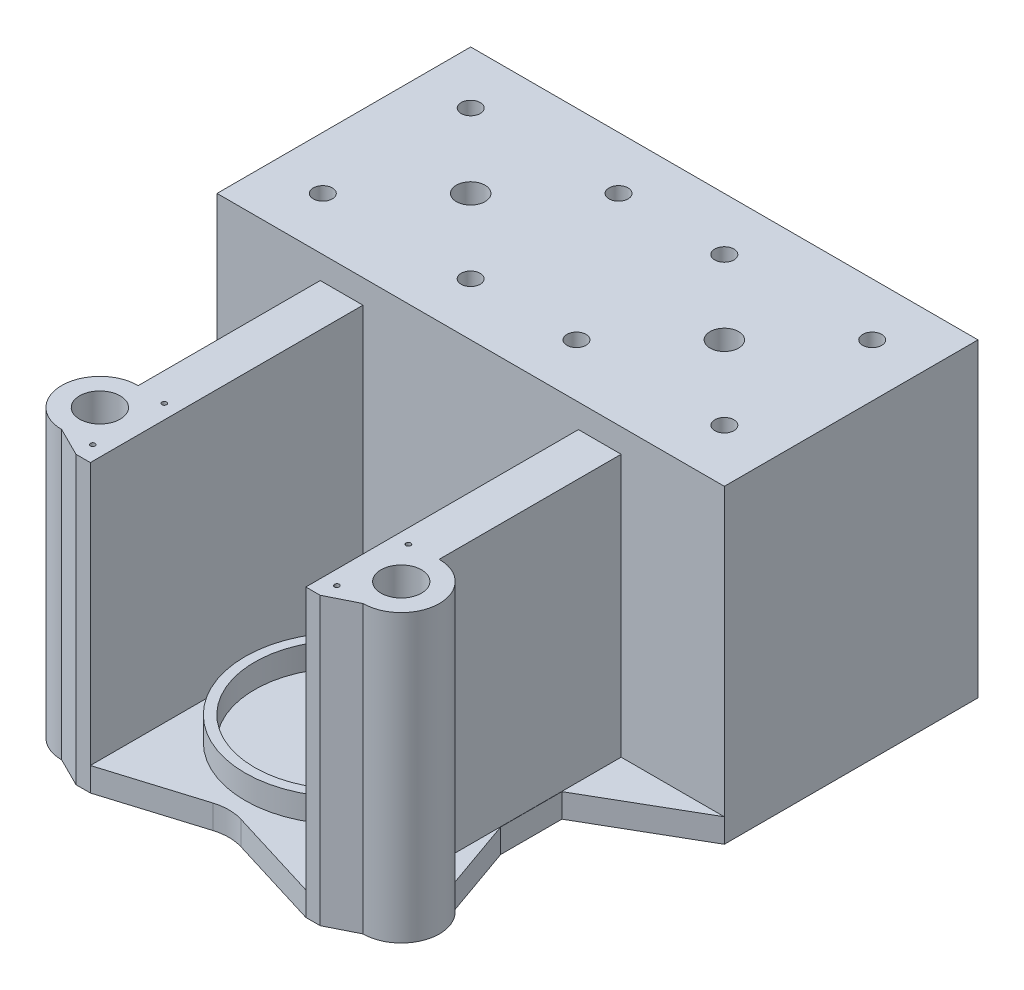
SolidWorks part; units mm, degrees
ref_plane "Front Plane" through (0, 0, 0) normal (0, 0, 1) x (1, 0, 0)
ref_plane "Top Plane" through (0, 0, 0) normal (0, 1, 0) x (1, 0, 0)
ref_plane "Right Plane" through (0, 0, 0) normal (1, 0, 0) x (0, 0, -1)
sketch "Sketch1" plane through (0, 0, 0) normal (0, 1, 0) x (1, 0, 0)
  circle A0 centre (0, 0) radius 21.15
  dimension "D1" = 42.3
extrude "Boss-Extrude1" add sketch "Sketch1" along normal blind 5
sketch "Sketch2" plane through (0, 0, 0) normal (0, 1, 0) x (1, 0, 0)
  circle A0 centre (0, 0) radius 19.15
  circle A1 centre (0, 0) radius 21.15
  dimension "D1" = 38.3
  dimension "D2" = 42.3
extrude "Boss-Extrude2" add sketch "Sketch2" along normal blind 10
sketch "Sketch3" plane through (0, 0, 0) normal (0, 1, 0) x (1, 0, 0)
  line L0 (48.18, 31.15) -> (5, 31.15)
  line L1 (-5, 74.33) -> (-48.18, 74.33)
  line L2 (-5, 74.33) -> (-5, 31.15)
  line L3 (-5, 31.15) -> (-48.18, 31.15)
  line L4 (-48.18, 74.33) -> (-48.18, 31.15)
  line L5 (-5, 74.33) -> (-48.18, 31.15) construction
  line L6 (-5, 31.15) -> (-48.18, 74.33) construction
  line L7 (5, 74.33) -> (5, 31.15)
  line L8 (48.18, 74.33) -> (5, 74.33)
  line L9 (48.18, 74.33) -> (48.18, 31.15)
  line L10 (0, 0) -> (0, 74.33) construction
  line L11 (0, 26.15) -> (-53.18, 26.15)
  line L12 (-53.18, 79.33) -> (-53.18, 26.15)
  line L13 (0, 79.33) -> (-53.18, 79.33)
  line L14 (0, 79.33) -> (0, 26.15)
  line L15 (53.18, 26.15) -> (0, 26.15)
  line L16 (0, 79.33) -> (0, 26.15)
  line L17 (53.18, 79.33) -> (0, 79.33)
  line L18 (53.18, 79.33) -> (53.18, 26.15)
  line L19 (-36.7936, -13.9236) -> (-31.59, 0.8326)
  line L20 (-31.59, 0.8326) -> (-31.59, 13.685)
  line L21 (-31.59, 13.685) -> (-53.18, 26.15)
  line L22 (-26.3864, -26.0764) -> (0, -21.15)
  line L23 (-26.3864, -26.0764) -> (-36.7936, -13.9236) construction
  line L24 (53.18, 26.15) -> (31.59, 13.685)
  line L25 (31.59, 13.685) -> (31.59, 0.8326)
  line L26 (31.59, 0.8326) -> (36.7936, -13.9236)
  line L27 (0, -21.15) -> (26.3864, -26.0764)
  line L28 (26.3864, -26.0764) -> (36.7936, -13.9236) construction
  circle A0 centre (0, 0) radius 21.15 construction
  circle A1 centre (-31.59, -20) radius 8
  circle A2 centre (31.59, -20) radius 8
  circle A3 centre (0, 0) radius 21.15
  point P0 (-26.59, 52.74)
  point P12 (0, 21.15)
  dimension "D8" = 16
  dimension "D1" = 43.18
  dimension "D2" = 43.18
  dimension "D4" = 5
  dimension "D5" = 5
  dimension "D6" = 10
  dimension "D9" = 5
  dimension "D10" = 20
  dimension "D11" = 120
  dimension "D12" = 120
  dimension "D13" = 120
  dimension "D14" = 120
  dimension "D15" = 120
  dimension "D16" = 120
  dimension "D7" = 5
  dimension "D3" = 2
extrude "Boss-Extrude4" add sketch "Sketch3" along normal blind 5 contours A2 | A1 | L18 L17 L14 L15 L8 L9 L0 L7 | L14 L13 L12 L11 L4 L1 L2 L3 | L22 A3 L27 A2 L26 L25 L24 L15 L11 L21 L20 L19 A1 | A3
sketch "Sketch4" plane through (0, 5, 0) normal (0, 1, 0) x (1, 0, 0)
  line L0 (48.18, 31.15) -> (5, 31.15) construction
  line L1 (48.18, 74.33) -> (48.18, 31.15) construction
  line L2 (48.18, 74.33) -> (5, 74.33) construction
  line L3 (5, 74.33) -> (5, 31.15) construction
  line L4 (-5, 31.15) -> (-48.18, 31.15) construction
  line L5 (-5, 74.33) -> (-5, 31.15) construction
  line L6 (-5, 74.33) -> (-48.18, 74.33) construction
  line L7 (-48.18, 74.33) -> (-48.18, 31.15) construction
  line L8 (48.18, 31.15) -> (5, 31.15)
  line L9 (48.18, 74.33) -> (48.18, 31.15)
  line L10 (48.18, 74.33) -> (5, 74.33)
  line L11 (5, 74.33) -> (5, 31.15)
  line L12 (-5, 31.15) -> (-48.18, 31.15)
  line L13 (-5, 74.33) -> (-5, 31.15)
  line L14 (-5, 74.33) -> (-48.18, 74.33)
  line L15 (-48.18, 74.33) -> (-48.18, 31.15)
  line L16 (0, 79.33) -> (-53.18, 79.33)
  line L17 (-53.18, 79.33) -> (-53.18, 26.15)
  line L18 (0, 26.15) -> (-53.18, 26.15)
  line L19 (0, 79.33) -> (0, 26.15)
  line L20 (0, 79.33) -> (0, 26.15)
  line L21 (53.18, 26.15) -> (0, 26.15)
  line L22 (53.18, 79.33) -> (53.18, 26.15)
  line L23 (53.18, 79.33) -> (0, 79.33)
  line L24 (-31.59, -28) -> (-31.59, -12) construction
  line L25 (-25.59, -9) -> (-25.59, -31)
  line L26 (-5.5, 0) -> (5.5, 0) construction
  line L28 (-31.59, -28) -> (-25.59, -31)
  line L29 (-31.59, -12) -> (-25.59, -9)
  line L30 (-25.59, -9) -> (-22.59, -9)
  line L31 (-22.59, -9) -> (-22.59, -31)
  line L32 (-22.59, -31) -> (-25.59, -31)
  line L33 (-31.59, -20) -> (-25.59, -20) construction
  line L34 (25.59, -9) -> (22.59, -9)
  line L35 (31.59, -12) -> (25.59, -9)
  line L36 (22.59, -31) -> (25.59, -31)
  line L37 (22.59, -9) -> (22.59, -31)
  line L38 (31.59, -28) -> (25.59, -31)
  circle A0 centre (-31.59, -20) radius 8
  circle A1 centre (31.59, -20) radius 8
  circle A2 centre (-31.59, -20) radius 4.25
  circle A3 centre (31.59, -20) radius 4.25
  circle A4 centre (-25.59, -12.5) radius 0.5
  circle A5 centre (-25.59, -27.5) radius 0.5
  circle A6 centre (25.59, -12.5) radius 0.5
  circle A7 centre (25.59, -27.5) radius 0.5
  line M5 (-26.3864, -26.0764) -> (0, -21.15)
  line M7 (0, -21.15) -> (26.3864, -26.0764)
  arc M8 (26.3864, -26.0764) -> (36.7936, -13.9236) centre (31.59, -20) ccw
  line M12 (53.18, 26.15) -> (53.18, 79.33)
  line M13 (53.18, 79.33) -> (-53.18, 79.33)
  line M14 (-53.18, 79.33) -> (-53.18, 26.15)
  arc M18 (-36.7936, -13.9236) -> (-26.3864, -26.0764) centre (-31.59, -20) ccw
  line M19 (-48.18, 31.15) -> (-48.18, 74.33)
  line M20 (-48.18, 74.33) -> (-5, 74.33)
  line M21 (-5, 74.33) -> (-5, 31.15)
  line M22 (-5, 31.15) -> (-48.18, 31.15)
  line M23 (5, 74.33) -> (48.18, 74.33)
  line M24 (48.18, 74.33) -> (48.18, 31.15)
  line M25 (48.18, 31.15) -> (5, 31.15)
  line M26 (5, 31.15) -> (5, 74.33)
  dimension "D2" = 8.5
  dimension "D3" = 16
  dimension "D9" = 1
  dimension "D4" = 15
  dimension "D5" = 22
  dimension "D6" = 6
  dimension "D7" = 7.5
  dimension "D8" = 3
  dimension "D1" = 5
extrude "Boss-Extrude5" add sketch "Sketch4" along normal blind 55 and the other way up to surface contours A1 A3 M8 | A0 A2 M18 | L19 L18 M13 M14 M22 M19 M20 M21 | L21 L19 M12 M13 M26 M23 M24 M25 | A1 L35 L34 L37 L36 L38 A6 A7 | A5 L25 A0 L28 | A5 L25 L32 L31 L30 A4 A0 | L25 A0 | A4 L25 L29 A0 | A5 L25 L32 L31 M5 | A0 L25 M5 | L38 L37 L36 A7 M8 M7
sketch "Sketch5" plane through (0, 5, 0) normal (0, 1, 0) x (1, 0, 0)
  circle A0 centre (-25.59, -27.5) radius 1.5666
  circle A1 centre (-25.59, -12.5) radius 1.3563
  circle A2 centre (25.59, -12.5) radius 1.3871
  circle A3 centre (25.59, -23.4098) radius 1.9451
extrude "Boss-Extrude6" add sketch "Sketch5" along normal blind 50
sketch "Sketch6" plane through (0, 60, 0) normal (0, 1, 0) x (1, 0, 0)
  line L0 (-48.18, 31.15) -> (-5, 74.33) construction
  line L1 (-5, 74.33) -> (5, 74.33) construction
  line L2 (5, 74.33) -> (48.18, 31.15) construction
  line L3 (48.18, 74.33) -> (5, 31.15) construction
  line L4 (5, 31.15) -> (-5, 31.15) construction
  line L5 (-5, 31.15) -> (-48.18, 74.33) construction
  line L6 (0, -5.5) -> (0, 5.5) construction
  line L7 (53.18, 79.33) -> (-53.18, 79.33)
  line L8 (53.18, 79.33) -> (53.18, 26.15)
  line L9 (53.18, 26.15) -> (-53.18, 26.15)
  line L10 (-53.18, 79.33) -> (-53.18, 26.15)
  circle A0 centre (-26.59, 52.74) radius 3
  circle A1 centre (26.59, 52.74) radius 3
  circle A2 centre (-42.09, 68.24) radius 2
  circle A3 centre (-11.09, 68.24) radius 2
  circle A4 centre (-11.09, 37.24) radius 2
  circle A5 centre (-42.09, 37.24) radius 2
  circle A6 centre (11.09, 68.24) radius 2
  circle A7 centre (11.09, 37.24) radius 2
  circle A8 centre (42.09, 37.24) radius 2
  circle A9 centre (42.09, 68.24) radius 2
  dimension "D1" = 6
  dimension "D2" = 6
  dimension "D3" = 4
  dimension "D6" = 31
  dimension "D4" = 2
  dimension "D5" = 2
extrude "Boss-Extrude7" add sketch "Sketch6" along normal blind 5
sketch "Sketch7" plane through (0, 0, -79.33) normal (0, 0, -1) x (-1, 0, 0)
  line L0 (-53.18, 0) -> (53.18, 0) construction
  line L1 (-39.18, 0) -> (-17.18, 0)
  line L2 (-39.18, 0) -> (-39.18, 23)
  line L3 (-39.18, 23) -> (-17.18, 23)
  line L4 (-17.18, 0) -> (-17.18, 23)
  line L5 (-53.18, 65) -> (-53.18, 0) construction
  line L6 (0, 5.5) -> (0, -5.5) construction
  line L7 (39.18, 0) -> (17.18, 0)
  line L8 (39.18, 0) -> (39.18, 23)
  line L9 (39.18, 23) -> (17.18, 23)
  line L10 (17.18, 0) -> (17.18, 23)
  dimension "D1" = 14
  dimension "D2" = 22
  dimension "D3" = 23
extrude "Cut-Extrude1" cut sketch "Sketch7" against normal blind 5
sketch "Sketch8" plane through (0, 60, 0) normal (0, 1, 0) x (1, 0, 0)
  line L0 (-31.5428, -13.152) -> (-31.5428, 26.15)
  line L1 (-53.18, 26.15) -> (53.18, 26.15) construction
  line L2 (-31.5428, 26.15) -> (-22.59, 26.15)
  line L3 (-22.59, 26.15) -> (-22.59, -9.8773)
  line L4 (-22.59, -9) -> (-22.59, -31) construction
  line L5 (-22.59, -9.8773) -> (-22.59, -11.1715)
  line L6 (-22.59, -9) -> (-22.59, -25.3676) construction
  line L7 (-22.59, -11.1715) -> (-31.5428, -13.152)
  line L8 (0, -5.5) -> (0, 5.5) construction
  line L9 (31.5428, 26.15) -> (22.59, 26.15)
  line L10 (31.5428, -13.152) -> (31.5428, 26.15)
  line L11 (22.59, -11.1715) -> (31.5428, -13.152)
  line L12 (22.59, -9.8773) -> (22.59, -11.1715)
  line L13 (22.59, 26.15) -> (22.59, -9.8773)
  line L14 (22.59, -9) -> (22.59, -31) construction
  dimension "D1" = 8.9528
extrude "Boss-Extrude8" add sketch "Sketch8" against normal up to surface (60 mm away) up to face at (0, 0, -28.3771)
sketch "Sketch9" plane through (0, 5, 0) normal (0, 1, 0) x (1, 0, 0)
  line L0 (-22.59, -31) -> (-2.9357, -24.9641)
  line L1 (2.9357, -24.9641) -> (22.59, -31)
  line L2 (-22.59, -25.3676) -> (0, -21.15) construction
  line L3 (0, -21.15) -> (22.59, -25.3676) construction
  line L4 (22.59, 26.15) -> (22.59, -31) construction
  line L5 (-22.59, 26.15) -> (-22.59, -31) construction
  line L6 (-22.59, -25.3676) -> (0, -21.15)
  line L7 (0, -21.15) -> (22.59, -25.3676)
  line L8 (22.59, 26.15) -> (22.59, -31)
  line L9 (-22.59, 26.15) -> (-22.59, -31)
  arc A0 (-2.9357, -24.9641) -> (2.9357, -24.9641) centre (0, -34.5235) cw
  line M4 (-22.59, -25.3676) -> (0, -21.15)
  line M6 (0, -21.15) -> (22.59, -25.3676)
  dimension "D1" = 10
extrude "Boss-Extrude9" add sketch "Sketch9" against normal up to surface (5 mm away) contours L0 A0 L1 L8 L9 M6 M4 up to face at (0, 0, -28.3771)
